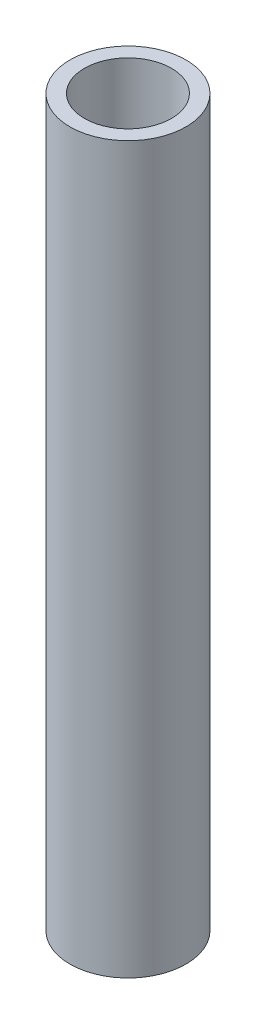
SolidWorks part; units mm, degrees
ref_plane "前视基准面" through (0, 0, 0) normal (0, 0, 1) x (1, 0, 0)
ref_plane "上视基准面" through (0, 0, 0) normal (0, 1, 0) x (1, 0, 0)
ref_plane "右视基准面" through (0, 0, 0) normal (1, 0, 0) x (0, 0, -1)
sketch "草图1" plane through (0, 0, 0) normal (0, 1, 0) x (1, 0, 0)
  circle A0 centre (0, 0) radius 1.5
  circle A1 centre (0, 0) radius 2
extrude "凸台-拉伸1" add sketch "草图1" along normal blind 25
